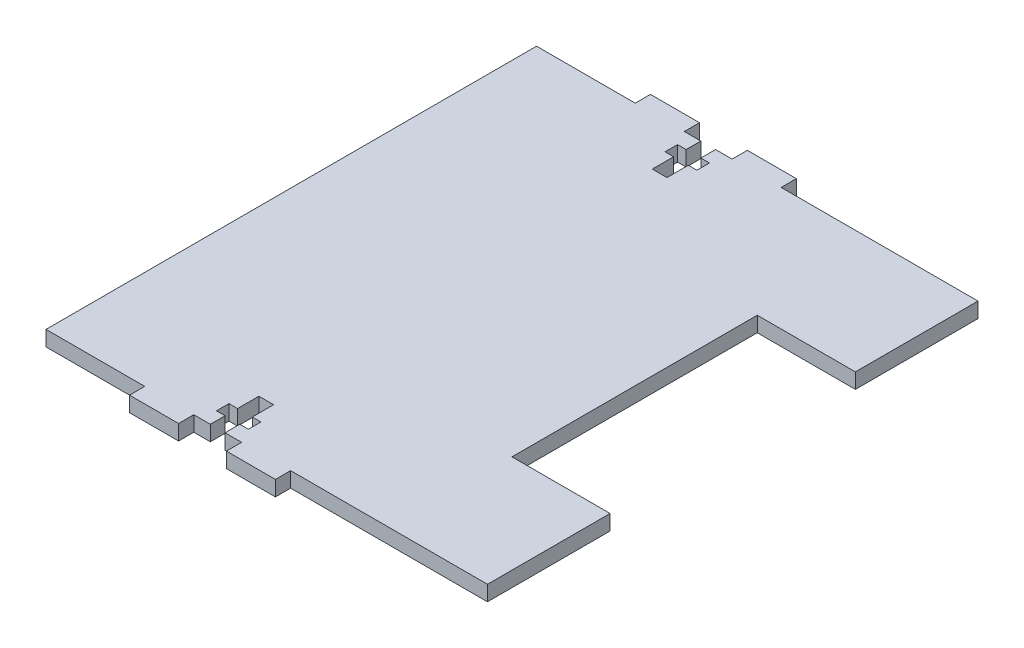
SolidWorks part; units mm, degrees
ref_plane "前视基准面" through (0, 0, 0) normal (0, 0, 1) x (1, 0, 0)
ref_plane "上视基准面" through (0, 0, 0) normal (0, 1, 0) x (1, 0, 0)
ref_plane "右视基准面" through (0, 0, 0) normal (1, 0, 0) x (0, 0, -1)
sketch "草图1" plane through (0, 0, 0) normal (0, 1, 0) x (1, 0, 0)
  line L0 (0, 50) -> (0, -50) construction
  line L1 (-35, -50) -> (35, -50)
  line L2 (-35, -50) -> (-35, 50)
  line L3 (-35, 50) -> (35, 50)
  line L4 (35, -50) -> (35, 50)
  line L5 (-35, -50) -> (35, 50) construction
  line L6 (-35, 50) -> (35, -50) construction
  line L7 (-4.875, -53.1) -> (-14.875, -53.1)
  line L8 (-14.875, -53.1) -> (-14.875, -50)
  line L9 (4.875, -53.1) -> (14.875, -53.1)
  line L10 (14.875, -53.1) -> (14.875, -50)
  line L11 (-35, 0) -> (35, 0) construction
  line L12 (14.875, 53.1) -> (14.875, 50)
  line L13 (4.875, 53.1) -> (14.875, 53.1)
  line L14 (-14.875, 53.1) -> (-14.875, 50)
  line L15 (-4.875, 53.1) -> (-14.875, 53.1)
  point P0 (0, 0)
  line B0 (0, -40.1) -> (0, -51.2019) construction
  line B1 (4.875, -53.1) -> (4.875, -50)
  line B2 (4.875, -50) -> (1.5, -50)
  line B3 (1.5, -50) -> (1.5, -47)
  line B4 (1.5, -47) -> (3.25, -47)
  line B5 (3.25, -47) -> (3.25, -44.45)
  line B6 (3.25, -44.45) -> (1.5, -44.45)
  line B7 (1.5, -44.45) -> (1.5, -40.1)
  line B8 (-1.5, -40.1) -> (1.5, -40.1)
  line B9 (-1.5, -44.45) -> (-1.5, -40.1)
  line B10 (-3.25, -44.45) -> (-1.5, -44.45)
  line B11 (-3.25, -47) -> (-3.25, -44.45)
  line B12 (-1.5, -47) -> (-3.25, -47)
  line B13 (-1.5, -50) -> (-1.5, -47)
  line B14 (-4.875, -50) -> (-1.5, -50)
  line B15 (-4.875, -53.1) -> (-4.875, -50)
  line B16 (0, 40.1) -> (0, 51.2019) construction
  line B17 (4.875, 53.1) -> (4.875, 50)
  line B18 (4.875, 50) -> (1.5, 50)
  line B19 (1.5, 50) -> (1.5, 47)
  line B20 (1.5, 47) -> (3.25, 47)
  line B21 (3.25, 47) -> (3.25, 44.45)
  line B22 (3.25, 44.45) -> (1.5, 44.45)
  line B23 (1.5, 44.45) -> (1.5, 40.1)
  line B24 (-1.5, 40.1) -> (1.5, 40.1)
  line B25 (-1.5, 44.45) -> (-1.5, 40.1)
  line B26 (-3.25, 44.45) -> (-1.5, 44.45)
  line B27 (-3.25, 47) -> (-3.25, 44.45)
  line B28 (-1.5, 47) -> (-3.25, 47)
  line B29 (-1.5, 50) -> (-1.5, 47)
  line B30 (-4.875, 50) -> (-1.5, 50)
  line B31 (-4.875, 53.1) -> (-4.875, 50)
  dimension "D1" = 100
  dimension "D2" = 70
  dimension "D3" = 10
  dimension "D4" = 10
sketch_block_instance "块2-11"
sketch_block "块2"
sketch_block_instance "块2-13"
extrude "凸台-拉伸1" add sketch "草图1" along normal blind 3.1 contours B29 L3 L2 L1 B13 B12 B11 B10 B9 B8 B7 B6 B5 B4 B3 L4 B19 B20 B21 B22 B23 B24 B25 B26 B27 B28 | B31 L15 L14 L3 | L13 B17 L3 L12 | L7 B15 L1 L8 | B1 L9 L10 L1
sketch "草图2" plane through (0, 0, 0) normal (0, 1, 0) x (1, 0, 0)
  line L0 (35, 50) -> (55, 50)
  line L1 (55, 50) -> (55, 25)
  line L2 (55, 25) -> (35, 25)
  line L3 (35, -50) -> (35, 50) construction
  line L4 (35, 50) -> (35, 25)
  line L5 (-42.6439, 0) -> (88.2869, 0) construction
  line L6 (35, -50) -> (35, -25)
  line L7 (55, -25) -> (35, -25)
  line L8 (55, -50) -> (55, -25)
  line L9 (35, -50) -> (55, -50)
  dimension "D1" = 20
  dimension "D2" = 25
extrude "凸台-拉伸2" add sketch "草图2" along normal blind 3.1
